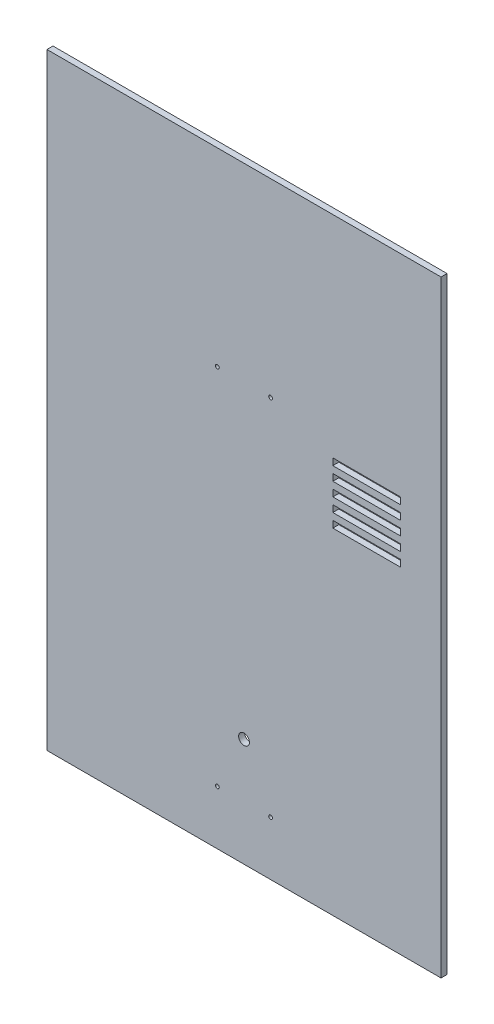
SolidWorks part; units mm, degrees
material "Acrylic (Medium-high impact)"
ref_plane "Front Plane" through (0, 0, 0) normal (0, 0, 1) x (1, 0, 0)
ref_plane "Top Plane" through (0, 0, 0) normal (0, 1, 0) x (1, 0, 0)
ref_plane "Right Plane" through (0, 0, 0) normal (1, 0, 0) x (0, 0, -1)
sketch "Sketch1" plane through (0, 0, 0) normal (0, 1, 0) x (1, 0, 0)
  line L1 (185, 2.8194) -> (-185, 2.8194)
  line L2 (185, 2.8194) -> (185, -2.8194)
  line L3 (185, -2.8194) -> (-185, -2.8194)
  line L4 (-185, 2.8194) -> (-185, -2.8194)
  line L5 (185, 2.8194) -> (-185, -2.8194) construction
  line L6 (185, -2.8194) -> (-185, 2.8194) construction
  point P0 (0, 0)
  dimension "D1" = 370
  dimension "D2" = 5.6388
extrude "Boss-Extrude1" add sketch "Sketch1" along normal blind 570
sketch "Sketch2" plane through (0, 0, 2.8194) normal (0, 0, 1) x (1, 0, 0)
  line L0 (-185, 0) -> (185, 0) construction
  line L1 (185, 570) -> (185, 0) construction
  circle A0 centre (0, 101.6) radius 5.08
  dimension "D1" = 10.16
  dimension "D2" = 101.6
  dimension "D3" = 185
extrude "Cut-Extrude1" cut sketch "Sketch2" against normal through all
sketch "Sketch3" plane through (0, 0, 2.8194) normal (0, 0, 1) x (1, 0, 0)
  line L0 (-185, 570) -> (-185, 0) construction
  line L1 (185, 570) -> (185, 0) construction
  line L2 (-185, 0) -> (185, 0) construction
  line L3 (-185, 570) -> (185, 570) construction
  circle A0 centre (-25, 50.8) radius 1.778
  circle A1 centre (25, 50.8) radius 1.778
  circle A2 centre (-25, 392) radius 1.778
  circle A3 centre (25, 392) radius 1.778
  dimension "D1" = 3.556
  dimension "D2" = 160
  dimension "D3" = 160
  dimension "D4" = 160
  dimension "D5" = 160
  dimension "D6" = 50.8
  dimension "D7" = 178
extrude "Cut-Extrude2" cut sketch "Sketch3" against normal through all
sketch "Sketch4" plane through (0, 0, 2.8194) normal (0, 0, 1) x (1, 0, 0)
  line L0 (185, 570) -> (185, 0) construction
  line L1 (83.4, 321.35) -> (146.9, 321.35)
  line L2 (83.4, 321.35) -> (83.4, 315)
  line L3 (83.4, 315) -> (146.9, 315)
  line L4 (146.9, 321.35) -> (146.9, 315)
  line L5 (-185, 0) -> (185, 0) construction
  dimension "D1" = 6.35
  dimension "D2" = 63.5
  dimension "D3" = 38.1
  dimension "D4" = 315
extrude "Cut-Extrude3" cut sketch "Sketch4" against normal through all
pattern_linear "LPattern1" count 5 spacing 12.7 along (0, 1, 0) of "Cut-Extrude3"
